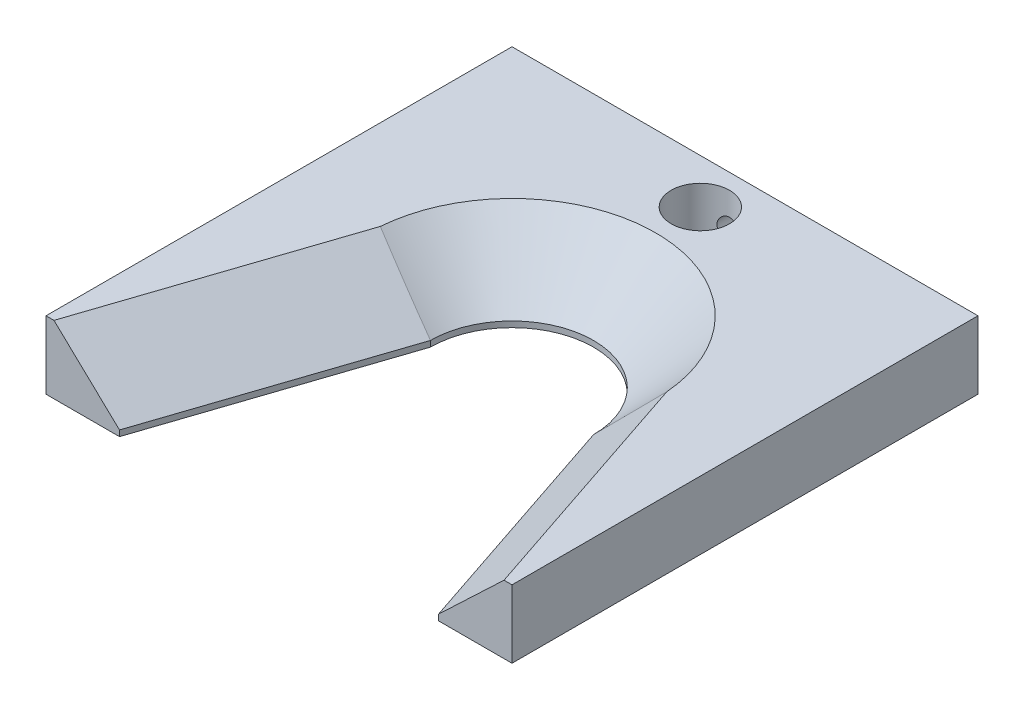
SolidWorks part; units mm, degrees
other "Markup1"
sketch "Sketch3" plane through (-63.5, 8.89, -38.1) normal (-0.9125, 0.4059, -0.0503) x (0.4069, 0.9134, -0.0121)
sketch "Sketch4" plane through (-63.5, 8.89, -38.1) normal (-0.9125, 0.4059, -0.0503) x (0.4069, 0.9134, -0.0121)
sketch "Sketch7" plane through (-63.5, 12.7, -38.1) normal (-0.9125, 0.4059, -0.0503) x (0.4069, 0.9134, -0.0121)
sketch "Sketch9" plane through (-63.5, 11.1125, -38.1) normal (-0.9125, 0.4059, -0.0503) x (0.4069, 0.9134, -0.0121)
sketch "Sketch12" plane through (-63.5, 11.1125, -38.1) normal (-0.9125, 0.4059, -0.0503) x (0.4069, 0.9134, -0.0121)
sketch "Sketch14" plane through (-38.1, 11.1125, -38.1) normal (-0.9125, 0.4059, -0.0503) x (0.4069, 0.9134, -0.0121)
sketch "Sketch16" plane through (-38.1, 11.1125, -38.1) normal (-0.9125, 0.4059, -0.0503) x (0.4069, 0.9134, -0.0121)
sketch "Sketch21" plane through (-38.1, 11.1125, -38.1) normal (-0.9125, 0.4059, -0.0503) x (0.4069, 0.9134, -0.0121)
sketch "Sketch23" plane through (-38.1, 11.1125, -38.1) normal (-0.9125, 0.4059, -0.0503) x (0.4069, 0.9134, -0.0121)
sketch "Sketch25" plane through (-38.1, 11.1125, -38.1) normal (-0.9125, 0.4059, -0.0503) x (0.4069, 0.9134, -0.0121)
other "Markup2"
sketch "Sketch6" plane through (-63.5, 8.89, -38.1) normal (-0.9404, 0.2221, -0.2575) x (0.2799, 0.9357, -0.215)
sketch "Sketch8" plane through (-63.5, 12.7, -38.1) normal (-0.9404, 0.2221, -0.2575) x (0.2799, 0.9357, -0.215)
sketch "Sketch10" plane through (-63.5, 11.1125, -38.1) normal (-0.9404, 0.2221, -0.2575) x (0.2799, 0.9357, -0.215)
sketch "Sketch13" plane through (-63.5, 11.1125, -38.1) normal (-0.9404, 0.2221, -0.2575) x (0.2799, 0.9357, -0.215)
sketch "Sketch15" plane through (-38.1, 11.1125, -38.1) normal (-0.9404, 0.2221, -0.2575) x (0.2799, 0.9357, -0.215)
sketch "Sketch17" plane through (-38.1, 11.1125, -38.1) normal (-0.9404, 0.2221, -0.2575) x (0.2799, 0.9357, -0.215)
sketch "Sketch22" plane through (-38.1, 11.1125, -38.1) normal (-0.9404, 0.2221, -0.2575) x (0.2799, 0.9357, -0.215)
sketch "Sketch24" plane through (-38.1, 11.1125, -38.1) normal (-0.9404, 0.2221, -0.2575) x (0.2799, 0.9357, -0.215)
sketch "Sketch26" plane through (-38.1, 11.1125, -38.1) normal (-0.9404, 0.2221, -0.2575) x (0.2799, 0.9357, -0.215)
material "1060 Alloy"
ref_plane "Front Plane" through (0, 0, 0) normal (0, 0, 1) x (1, 0, 0)
ref_plane "Top Plane" through (0, 0, 0) normal (0, 1, 0) x (1, 0, 0)
ref_plane "Right Plane" through (0, 0, 0) normal (1, 0, 0) x (0, 0, -1)
sketch "Sketch1" plane through (0, 0, 0) normal (0, 1, 0) x (1, 0, 0)
  line L0 (-13.335, 0) -> (-26.0831, -38.1)
  line L1 (38.1, 38.1) -> (-38.1, 38.1)
  line L2 (38.1, 38.1) -> (38.1, -38.1)
  line L3 (38.1, -38.1) -> (-38.1, -38.1)
  line L4 (-38.1, 38.1) -> (-38.1, -38.1)
  line L5 (38.1, 38.1) -> (-38.1, -38.1) construction
  line L6 (38.1, -38.1) -> (-38.1, 38.1) construction
  line L7 (13.335, 0) -> (26.0831, -38.1)
  circle A0 centre (0, 0) radius 13.335
  point P0 (0, 0)
  dimension "D3" = 26.67
  dimension "D1" = 76.2
  dimension "D2" = 76.2
  dimension "D4" = 37
extrude "Boss-Extrude1" add sketch "Sketch1" along normal blind 11.1125 contours A0 L7 L3 L2 L1 L4 L0
chamfer "Chamfer1" distance 10.16 angle 45 3 edges at (19.709, 11.1125, 19.05) (0, 11.1125, -13.335) (-19.709, 11.1125, 19.05)
sketch "Sketch18" plane through (0, 0, -38.1) normal (0, 0, -1) x (-1, 0, 0)
  line L0 (-38.1, 5.5562) -> (38.1, 5.5562) construction
  line L1 (-38.1, 11.1125) -> (-38.1, 0) construction
  line L2 (38.1, 11.1125) -> (38.1, 0) construction
  line L3 (0, 0) -> (0, 11.1125) construction
  line L4 (-38.1, 11.1125) -> (38.1, 11.1125) construction
  point P11 (0, 5.5562)
hole_wizard "Tap Drill for #8-32 Tap1" positions "3DSketch5" profile "Sketch20" hole size "#8-32" standard "ANSI Inch"
sketch3d "3DSketch5"
  point P0 (0, 5.5562, -38.1)
sketch "Sketch20" plane through (0, 5.5562, -38.1) normal (1, 0, 0) x (0, 1, 0)
  line L0 (0, 0) -> (0, 13.7378)
  line L1 (0, 13.7378) -> (1.7272, 12.7)
  line L2 (1.7272, 12.7) -> (1.7272, 0)
  line L5 (1.7272, 0) -> (0, 0)
  line L10 (0, 13.7378) -> (-1.7272, 12.7) construction
  line L11 (0, -6.35) -> (0, 107.95) construction
  dimension "Hole Dia." = 3.4544
  dimension "Hole Depth" = 12.7
  dimension "Drill Angle" = 118
sketch "Sketch27" plane through (0, 11.1125, 0) normal (0, 1, 0) x (1, 0, 0)
  line L0 (0, 38.1) -> (0, 23.495) construction
  line L1 (38.1, 38.1) -> (-38.1, 38.1) construction
  arc A0 (23.4197, 1.8798) -> (-23.4197, 1.8798) centre (0, 0) ccw construction
  circle A1 centre (0, 30.7975) radius 4.7625
  dimension "D1" = 9.525
extrude "Cut-Extrude1" cut sketch "Sketch27" against normal through all
